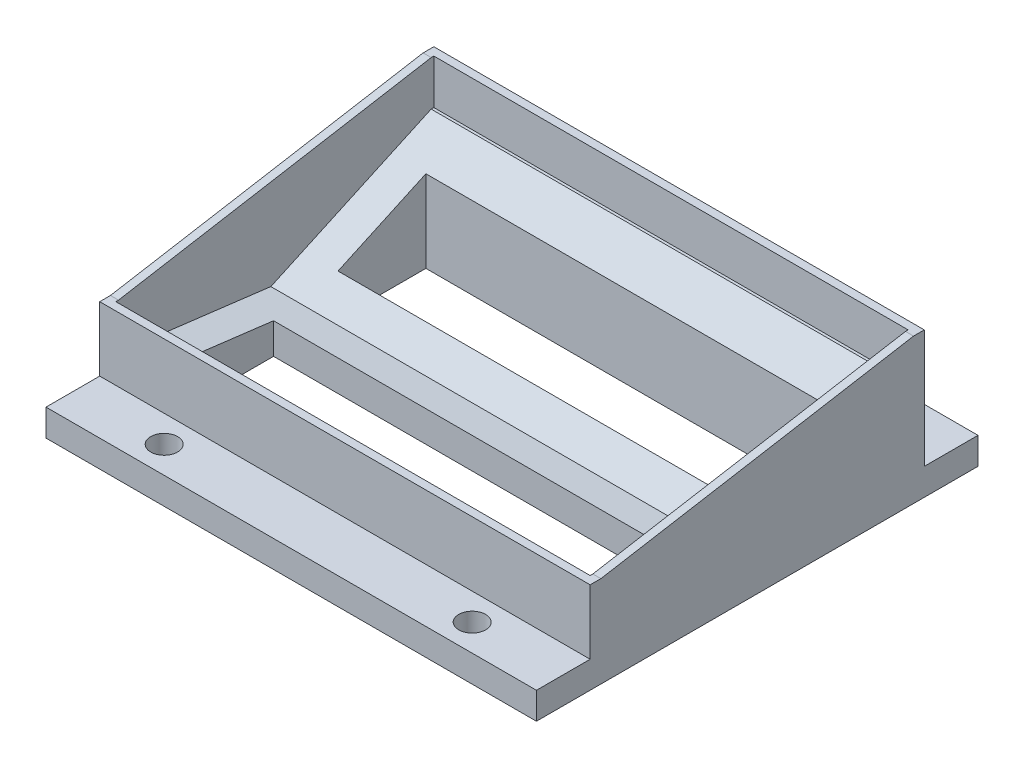
SolidWorks part; units mm, degrees
ref_plane "Front Plane" through (0, 0, 0) normal (0, 0, 1) x (1, 0, 0)
ref_plane "Top Plane" through (0, 0, 0) normal (0, 1, 0) x (1, 0, 0)
ref_plane "Right Plane" through (0, 0, 0) normal (1, 0, 0) x (0, 0, -1)
sketch "Sketch1" plane through (0, 0, 0) normal (1, 0, 0) x (0, 0, -1)
  line L0 (-73.5515, 26.9468) -> (-43.7115, 40.6401)
  line L1 (-43.7115, 40.6401) -> (-43.7115, 26.9468)
  line L2 (-43.7115, 26.9468) -> (-31.7115, 26.9468)
  line L3 (-31.7115, 26.9468) -> (-31.7115, 21.9468)
  line L4 (-31.7115, 21.9468) -> (-113.9115, 21.9468)
  line L5 (-113.9115, 21.9468) -> (-113.9115, 26.9468)
  line L6 (-113.9115, 26.9468) -> (-101.9115, 26.9468)
  line L7 (-101.9115, 26.9468) -> (-101.9115, 30.4642)
  line L8 (-101.9115, 30.4642) -> (-73.5515, 26.9468)
  line L9 (-73.5515, 26.9468) -> (-16.7383, 26.9468) construction
  line L10 (-73.5515, 26.9468) -> (-129.2153, 26.9468) construction
  point P11 (-145.4805, 40.1322)
  dimension "D1" = 24.65
  dimension "D2" = 7.07
  dimension "D3" = 28.36
  dimension "D4" = 29.84
  dimension "D5" = 12
  dimension "D6" = 12
  dimension "D7" = 0
  dimension "D8" = 5
extrude "Boss-Extrude1" add sketch "Sketch1" along normal blind 87.3
sketch "Sketch2" plane through (0, 26.9468, 0) normal (0, 1, 0) x (1, 0, 0)
  line L0 (0, -31.7115) -> (0, -43.7115) construction
  line L1 (87.3, -31.7115) -> (0, -31.7115) construction
  line L2 (87.3, -113.9115) -> (0, -113.9115) construction
  line L3 (87.3, -31.7115) -> (87.3, -43.7115) construction
  circle A0 centre (15, -36.7115) radius 2.5
  circle A1 centre (72.3334, -36.7115) radius 2.5
  circle A2 centre (72.3334, -108.9115) radius 2.5
  circle A3 centre (15, -108.9115) radius 2.5
  point P2 (0, -37.7115)
  point P15 (87.3, -37.7115)
  dimension "D1" = 5
  dimension "D2" = 15
  dimension "D3" = 5
  dimension "D6" = 5
  dimension "D7" = 15
  dimension "D4" = 2
  dimension "D5" = 2
extrude "Cut-Extrude1" cut sketch "Sketch2" against normal up to next
sketch "Sketch3" plane through (0, 21.9468, 0) normal (0, -1, 0) x (1, 0, 0)
  line L0 (6, 95.9115) -> (6, 79.5515)
  line L1 (6, 79.5515) -> (81.3, 79.5515)
  line L2 (81.3, 79.5515) -> (81.3, 95.9115)
  line L3 (81.3, 95.9115) -> (6, 95.9115)
  line L4 (0, 113.9115) -> (0, 31.7115) construction
  line L5 (87.3, 113.9115) -> (87.3, 31.7115) construction
  line L6 (87.3, 73.5515) -> (0, 73.5515) construction
  line L7 (87.3, 101.9115) -> (0, 101.9115) construction
  line L8 (81.3, 51.1915) -> (6, 51.1915)
  line L9 (81.3, 67.5515) -> (81.3, 51.1915)
  line L10 (6, 67.5515) -> (81.3, 67.5515)
  line L11 (6, 51.1915) -> (6, 67.5515)
  dimension "D1" = 6
  dimension "D2" = 6
  dimension "D3" = 6
  dimension "D4" = 6
extrude "Cut-Extrude2" cut sketch "Sketch3" against normal through all
sketch "Sketch4" plane through (87.3, 0, 0) normal (1, 0, 0) x (0, 0, -1)
  line L0 (-101.9115, 26.9468) -> (-101.9115, 38.9468)
  line L1 (-101.9115, 38.9468) -> (-103.9115, 38.9468)
  line L2 (-103.9115, 38.9468) -> (-103.9115, 26.9468)
  line L3 (-101.9115, 26.9468) -> (-113.9115, 26.9468) construction
  line L4 (-103.9115, 26.9468) -> (-101.9115, 26.9468)
  line L5 (-43.7115, 26.9468) -> (-43.7115, 48.9468)
  line L6 (-43.7115, 48.9468) -> (-41.7115, 48.9468)
  line L7 (-41.7115, 48.9468) -> (-41.7115, 26.9468)
  line L8 (-31.7115, 26.9468) -> (-43.7115, 26.9468) construction
  line L9 (-41.7115, 26.9468) -> (-43.7115, 26.9468)
  dimension "D1" = 12
  dimension "D2" = 2
  dimension "D3" = 2
  dimension "D4" = 22
extrude "Boss-Extrude2" add sketch "Sketch4" against normal through all
sketch "Sketch8" plane through (87.3, 0, 0) normal (1, 0, 0) x (0, 0, -1)
  line L0 (-103.9115, 38.9468) -> (-101.9115, 38.9468)
  line L1 (-101.9115, 38.9468) -> (-43.7115, 48.9468)
  line L2 (-43.7115, 48.9468) -> (-41.7115, 48.9468)
  line L3 (-41.7115, 48.9468) -> (-41.7115, 26.9468)
  line L4 (-41.7115, 26.9468) -> (-31.7115, 26.9468)
  line L5 (-31.7115, 26.9468) -> (-31.7115, 21.9468)
  line L6 (-31.7115, 21.9468) -> (-113.9115, 21.9468)
  line L7 (-113.9115, 21.9468) -> (-113.9115, 26.9468)
  line L8 (-113.9115, 26.9468) -> (-103.9115, 26.9468)
  line L9 (-103.9115, 26.9468) -> (-103.9115, 38.9468)
extrude "Boss-Extrude16" add sketch "Sketch8" along normal blind 2
pattern_linear "LPattern1" count 2 spacing 89.3 along (-1, 0, 0) of "Boss-Extrude16"
sketch "Sketch12" plane through (0, 0, 0) normal (1, 0, 0) x (0, 0, -1)
  line L0 (-43.7115, 48.9468) -> (-43.7115, 40.6401)
  line L1 (-43.7115, 40.6401) -> (-73.5515, 26.9468)
  line L2 (-73.5515, 26.9468) -> (-101.9115, 30.4642)
  line L3 (-101.9115, 30.4642) -> (-101.9115, 38.9468)
  line L4 (-101.9115, 38.9468) -> (-43.7115, 48.9468)
extrude "Cut-Extrude4" cut sketch "Sketch12" against normal blind 0.5
sketch "Sketch13" plane through (87.3, 0, 0) normal (-1, 0, 0) x (0, 0, 1)
  line L0 (43.7115, 40.6401) -> (43.7115, 48.9468)
  line L1 (43.7115, 48.9468) -> (101.9115, 38.9468)
  line L2 (101.9115, 38.9468) -> (101.9115, 30.4642)
  line L3 (101.9115, 30.4642) -> (73.5515, 26.9468)
  line L4 (73.5515, 26.9468) -> (43.7115, 40.6401)
extrude "Cut-Extrude5" cut sketch "Sketch13" against normal blind 0.5
sketch "Sketch14" plane through (0, 0, 43.7115) normal (0, 0, 1) x (1, 0, 0)
  line L0 (-0.5, 48.9468) -> (-0.5, 40.6401)
  line L1 (-0.5, 40.6401) -> (87.8, 40.6401)
  line L2 (87.8, 40.6401) -> (87.8, 48.9468)
  line L3 (87.8, 48.9468) -> (-0.5, 48.9468)
extrude "Cut-Extrude6" cut sketch "Sketch14" against normal blind 0.5
sketch "Sketch15" plane through (0, 0, 101.9115) normal (0, 0, -1) x (-1, 0, 0)
  line L1 (0.5, 38.9468) -> (-87.8, 38.9468)
  line L2 (0.5, 38.9468) -> (0.5, 30.4642)
  line L3 (0.5, 30.4642) -> (-87.8, 30.4642)
  line L4 (-87.8, 38.9468) -> (-87.8, 30.4642)
extrude "Cut-Extrude7" cut sketch "Sketch15" against normal blind 0.5
